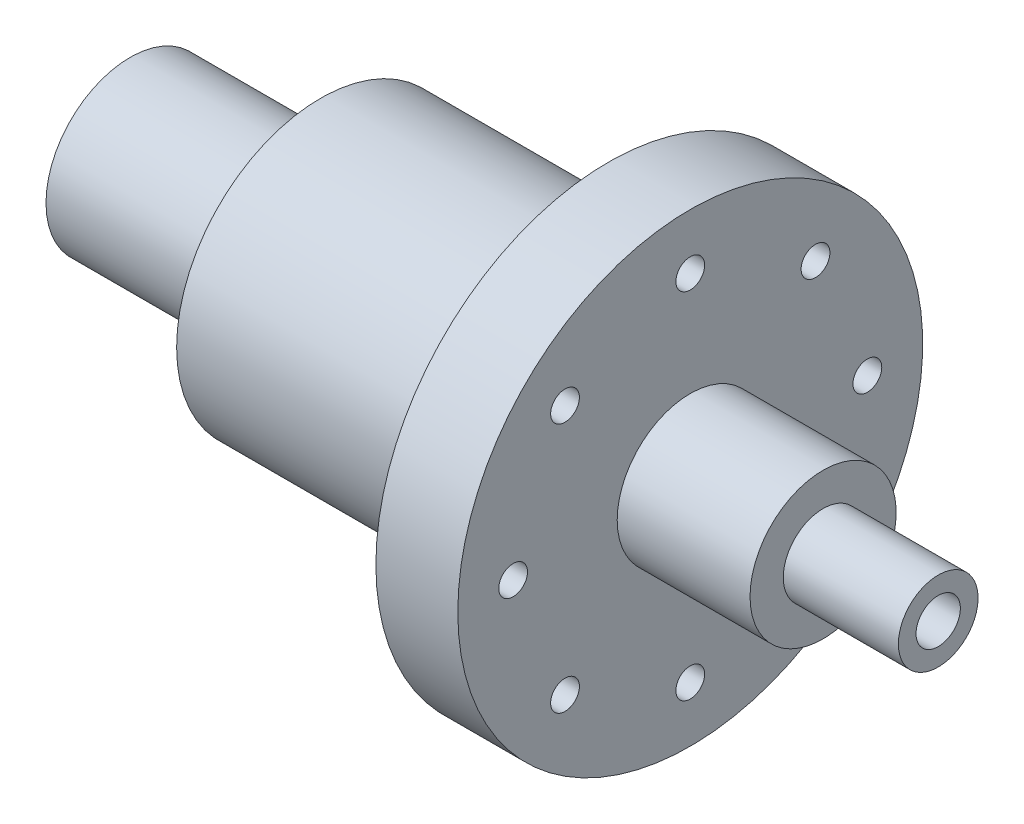
SolidWorks part; units mm, degrees
ref_plane "Front Plane" through (0, 0, 0) normal (0, 0, 1) x (1, 0, 0)
ref_plane "Top Plane" through (0, 0, 0) normal (0, 1, 0) x (1, 0, 0)
ref_plane "Right Plane" through (0, 0, 0) normal (1, 0, 0) x (0, 0, -1)
sketch "Sketch1" plane through (0, 0, 0) normal (0, 0, 1) x (1, 0, 0)
  line L0 (-194.0696, 0) -> (211.4405, 0) construction
  line L1 (-182.5, 10) -> (-182.5, 38)
  line L2 (-182.5, 38) -> (-96.5, 38)
  line L3 (-96.5, 38) -> (-96.5, 65)
  line L4 (-96.5, 65) -> (33.5, 65)
  line L5 (33.5, 65) -> (33.5, 105)
  line L6 (33.5, 105) -> (70.5, 105)
  line L7 (70.5, 105) -> (70.5, 33)
  line L8 (70.5, 33) -> (130.5, 33)
  line L9 (130.5, 33) -> (130.5, 18)
  line L10 (130.5, 18) -> (182.5, 18)
  line L11 (182.5, 18) -> (182.5, 10)
  line L12 (182.5, 10) -> (-182.5, 10)
  point P5 (0, 10)
  dimension "D1" = 86
  dimension "D2" = 216
  dimension "D3" = 365
  dimension "D4" = 60
  dimension "D5" = 112
  dimension "D6" = 8
  dimension "D7" = 15
  dimension "D8" = 40
  dimension "D9" = 28
  dimension "D10" = 27
  dimension "D11" = 40
  dimension "D12" = 10
revolve "Revolve1" add sketch "Sketch1" angle 360 about L0
sketch "Sketch2" plane through (70.5, 0, 0) normal (1, 0, 0) x (0, 0, -1)
  circle A0 centre (0, 80) radius 6.5
  circle A1 centre (56.5685, 56.5685) radius 6.5
  circle A2 centre (80, 0) radius 6.5
  circle A3 centre (56.5685, -56.5685) radius 6.5
  circle A4 centre (0, -80) radius 6.5
  circle A5 centre (-56.5685, -56.5685) radius 6.5
  circle A6 centre (-80, 0) radius 6.5
  circle A7 centre (-56.5685, 56.5685) radius 6.5
  point P18 (0, 0)
  dimension "D1" = 13
  dimension "D3" = 80
  dimension "D2" = 8
extrude "Cut-Extrude1" cut sketch "Sketch2" against normal through all
sketch "Sketch3" plane through (0, 0, 0) normal (1, 0, 0) x (0, 0, -1)
  line L0 (0, 0) -> (-175.6947, -1.8127)
  line L1 (-175.6947, -1.8127) -> (-2.6314, 255.0473)
  line L2 (-2.6314, 255.0473) -> (0, 0)
